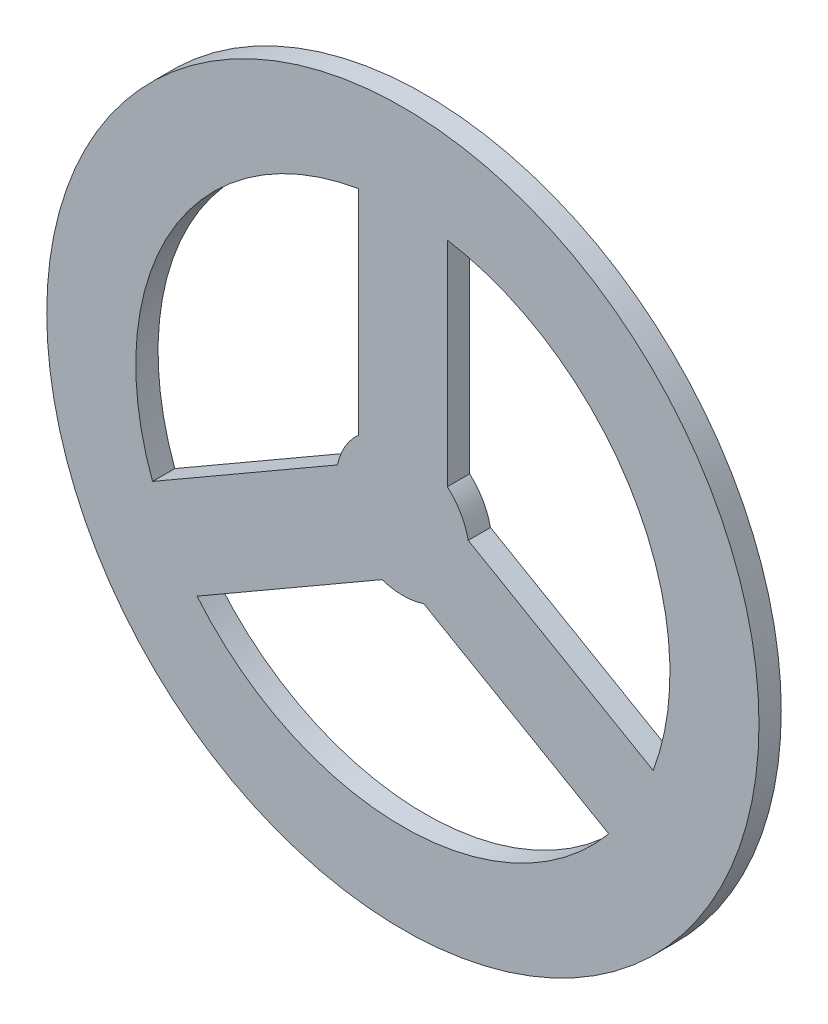
SolidWorks part; units mm, degrees
ref_plane "Front Plane" through (0, 0, 0) normal (0, 0, 1) x (1, 0, 0)
ref_plane "Top Plane" through (0, 0, 0) normal (0, 1, 0) x (1, 0, 0)
ref_plane "Right Plane" through (0, 0, 0) normal (1, 0, 0) x (0, 0, -1)
sketch "Sketch1" plane through (0, 0, 0) normal (0, 0, 1) x (1, 0, 0)
  line L1 (-12.7, 14.199) -> (-12.7, 75.1342)
  line L2 (12.7, 14.199) -> (12.7, 75.1342)
  line L4 (18.6467, 3.899) -> (71.4181, -26.5686)
  line L5 (5.9467, -18.098) -> (58.7181, -48.5656)
  line L6 (-5.9467, -18.098) -> (-58.7181, -48.5656)
  line L7 (-18.6467, 3.899) -> (-71.4181, -26.5686)
  arc A0 (-12.7, 14.199) -> (-18.6467, 3.899) centre (0, 0) ccw
  circle A1 centre (0, 0) radius 101.6
  arc A2 (-12.7, 75.1342) -> (-71.4181, -26.5686) centre (0, 0) ccw
  arc A3 (-58.7181, -48.5656) -> (58.7181, -48.5656) centre (0, 0) ccw
  arc A4 (-5.9467, -18.098) -> (5.9467, -18.098) centre (0, 0) ccw
  arc A5 (18.6467, 3.899) -> (12.7, 14.199) centre (0, 0) ccw
  arc A6 (71.4181, -26.5686) -> (12.7, 75.1342) centre (0, 0) ccw
  point P21 (0, 0)
  dimension "D1" = 38.1
  dimension "D2" = 203.2
  dimension "D3" = 152.4
  dimension "D4" = 3
extrude "Boss-Extrude1" add sketch "Sketch1" along normal blind 6.35
scale "Scale1" scale about centroid uniform scaling yes scale factor 0.5
